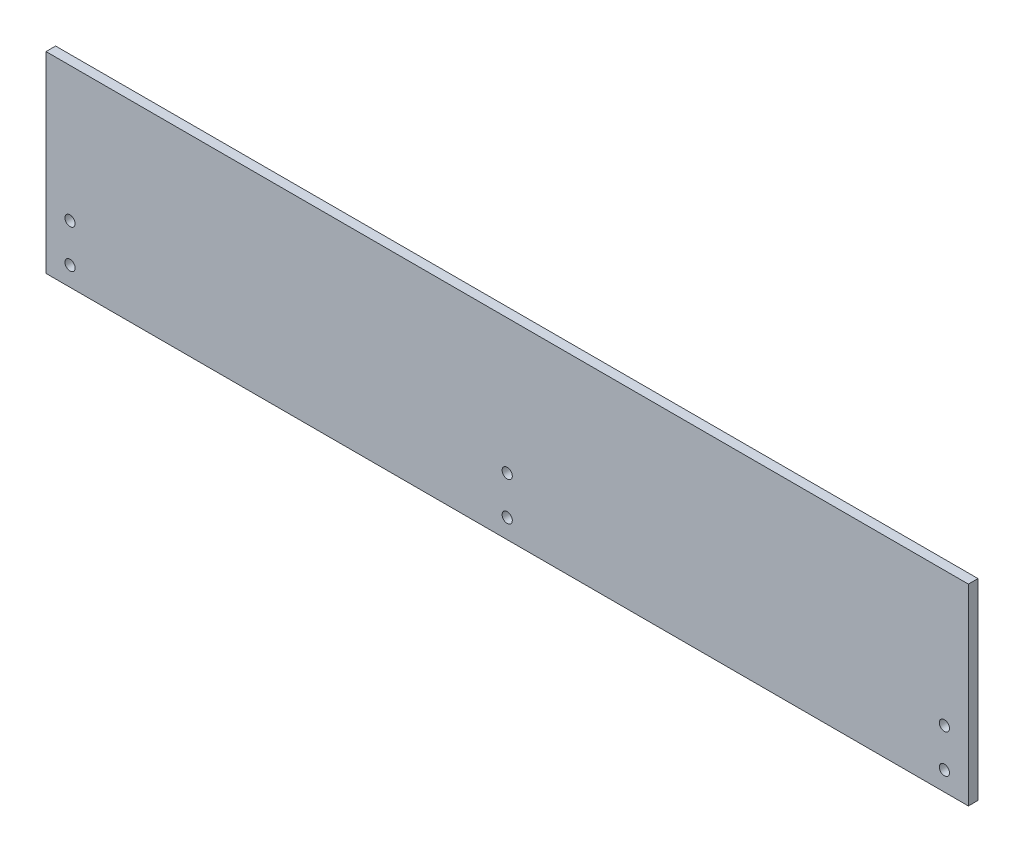
SolidWorks part; units mm, degrees
ref_plane "Front Plane" through (0, 0, 0) normal (0, 0, 1) x (1, 0, 0)
ref_plane "Top Plane" through (0, 0, 0) normal (0, 1, 0) x (1, 0, 0)
ref_plane "Right Plane" through (0, 0, 0) normal (1, 0, 0) x (0, 0, -1)
sketch "Sketch2" plane through (0, 0, 0) normal (0, 0, 1) x (1, 0, 0)
  line L1 (0, 0) -> (609.6, 0)
  line L2 (0, 0) -> (0, 127)
  line L3 (0, 127) -> (609.6, 127)
  line L4 (609.6, 0) -> (609.6, 127)
  dimension "D1" = 127
  dimension "D2" = 609.6
extrude "Boss-Extrude1" add sketch "Sketch2" along normal blind 6.35
sketch "Sketch3" plane through (0, 0, 6.35) normal (0, 0, 1) x (1, 0, 0)
  line L0 (0, 127) -> (0, 0) construction
  line L1 (0, 0) -> (609.6, 0) construction
  line L2 (609.6, 0) -> (609.6, 127) construction
  circle A0 centre (15.875, 12.7) radius 3.3655
  circle A2 centre (593.725, 12.7) radius 3.3655
  circle A3 centre (593.725, 38.1) radius 3.3655
  circle A4 centre (15.875, 38.1) radius 3.3655
  dimension "D3" = 6.731
  dimension "D4" = 12.7
  dimension "D2" = 6.731
  dimension "D6" = 15.875
  dimension "D7" = 6.731
  dimension "D9" = 6.731
  dimension "D1" = 15.875
  dimension "D5" = 12.7
  dimension "D8" = 25.4
  dimension "D10" = 25.4
  dimension "D11" = 15.875
  dimension "D12" = 15.875
extrude "Cut-Extrude1" cut sketch "Sketch3" against normal blind 6.35
sketch "Sketch4" plane through (0, 0, 0) normal (0, 0, -1) x (-1, 0, 0)
  line L0 (0, 127) -> (0, 0) construction
  line L1 (-609.6, 127) -> (0, 127) construction
  circle A0 centre (-3.18, 123) radius 1.143
  dimension "D2" = 4
  dimension "D3" = 2.286
  dimension "D1" = 3.18
sketch "Sketch5" plane through (0, 0, 0) normal (0, 0, -1) x (-1, 0, 0)
  line L0 (0, 0) -> (-609.6, 0) construction
  line L1 (0, 127) -> (0, 0) construction
  circle A0 centre (-3.18, 41.3) radius 1.143
  dimension "D3" = 2.286
  dimension "D1" = 41.3
  dimension "D2" = 3.18
sketch "Sketch6" plane through (0, 0, 6.35) normal (0, 0, 1) x (1, 0, 0)
  line L0 (0, 0) -> (609.6, 0) construction
  line L1 (0, 127) -> (0, 0) construction
  circle A0 centre (304.8, 38.1) radius 3.3655
  circle A1 centre (304.8, 12.7) radius 3.3655
  dimension "D1" = 6.731
  dimension "D2" = 6.731
  dimension "D3" = 25.4
  dimension "D4" = 12.7
  dimension "D5" = 304.8
extrude "Cut-Extrude4" cut sketch "Sketch6" against normal through all
